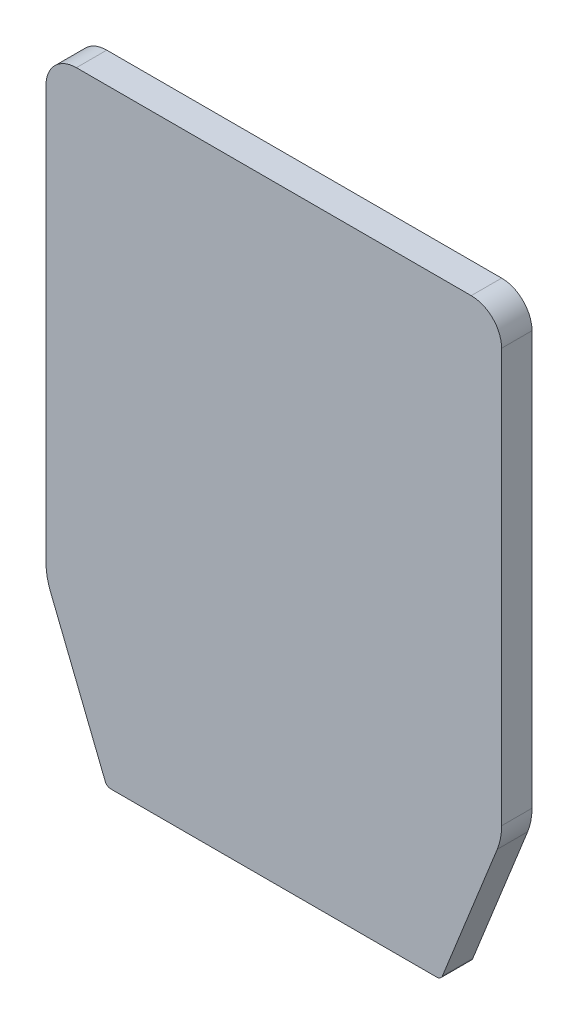
SolidWorks part; units mm, degrees
ref_plane "Front Plane" through (0, 0, 0) normal (0, 0, 1) x (1, 0, 0)
ref_plane "Top Plane" through (0, 0, 0) normal (0, 1, 0) x (1, 0, 0)
ref_plane "Right Plane" through (0, 0, 0) normal (1, 0, 0) x (0, 0, -1)
sketch "Sketch-lid body" plane through (0, 0, 0) normal (0, 0, 1) x (1, 0, 0)
  line L0 (55.5029, 1.2572) -> (73.5695, 46.4238) construction
  line L1 (-53.6459, 0) -> (53.6459, 0) construction
  line L2 (-73.5695, 46.4238) -> (-55.5029, 1.2572) construction
  line L3 (-75, 190) -> (-75, 53.8516) construction
  line L4 (-65, 200) -> (65, 200) construction
  line L5 (75, 190) -> (75, 53.8516) construction
  line L6 (55.5029, 1.2572) -> (73.5695, 46.4238)
  line L7 (-53.6459, 0) -> (53.6459, 0)
  line L8 (-73.5695, 46.4238) -> (-55.5029, 1.2572)
  line L9 (-75, 190) -> (-75, 53.8516)
  line L10 (-65, 200) -> (65, 200)
  line L11 (75, 190) -> (75, 53.8516)
  arc A0 (73.5695, 46.4238) -> (75, 53.8516) centre (55, 53.8516) ccw construction
  arc A1 (53.6459, 0) -> (55.5029, 1.2572) centre (53.6459, 2) ccw construction
  arc A2 (-55.5029, 1.2572) -> (-53.6459, 0) centre (-53.6459, 2) ccw construction
  arc A3 (-75, 53.8516) -> (-73.5695, 46.4238) centre (-55, 53.8516) ccw construction
  arc A4 (-65, 200) -> (-75, 190) centre (-65, 190) ccw construction
  arc A5 (75, 190) -> (65, 200) centre (65, 190) ccw construction
  arc A6 (73.5695, 46.4238) -> (75, 53.8516) centre (55, 53.8516) ccw
  arc A7 (53.6459, 0) -> (55.5029, 1.2572) centre (53.6459, 2) ccw
  arc A8 (-55.5029, 1.2572) -> (-53.6459, 0) centre (-53.6459, 2) ccw
  arc A9 (-75, 53.8516) -> (-73.5695, 46.4238) centre (-55, 53.8516) ccw
  arc A10 (-65, 200) -> (-75, 190) centre (-65, 190) ccw
  arc A11 (75, 190) -> (65, 200) centre (65, 190) ccw
extrude "Boss-Extrude1" add sketch "Sketch-lid body" along normal blind 10
